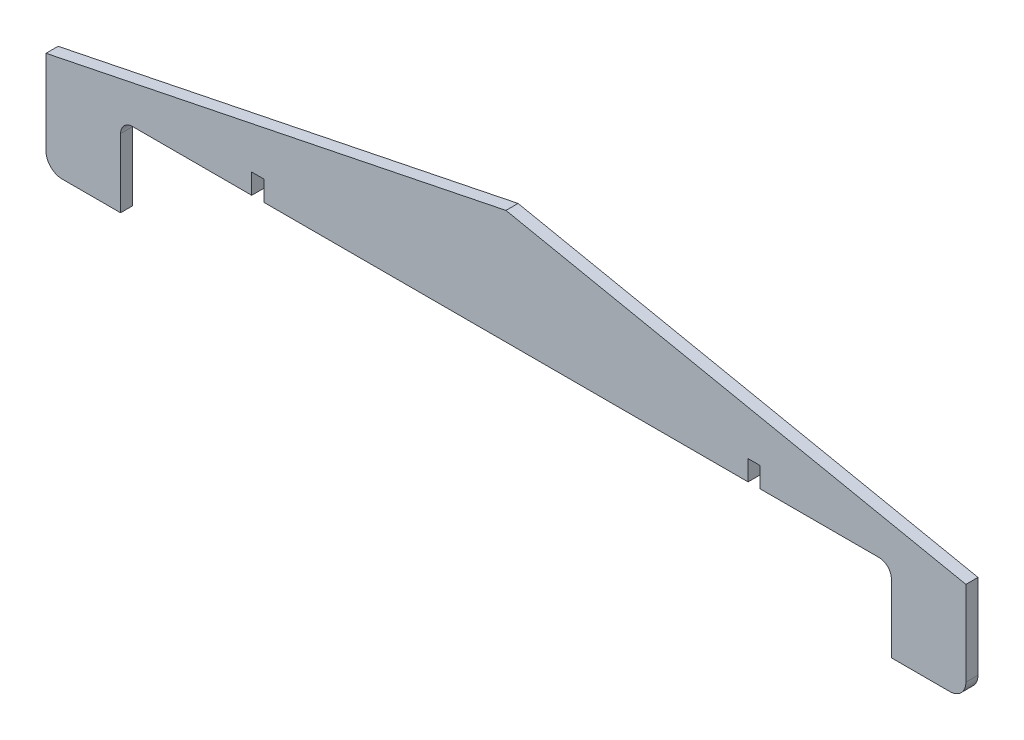
SolidWorks part; units mm, degrees
ref_plane "Front Plane" through (0, 0, 0) normal (0, 0, 1) x (1, 0, 0)
ref_plane "Top Plane" through (0, 0, 0) normal (0, 1, 0) x (1, 0, 0)
ref_plane "Right Plane" through (0, 0, 0) normal (1, 0, 0) x (0, 0, -1)
sketch "Sketch1" plane through (0, 0, 0) normal (0, 0, 1) x (1, 0, 0)
  line L0 (0, 0) -> (0, 19.9998) construction
  line L1 (-16, 19.9998) -> (16, 19.9998)
  line L2 (-113.9796, 0) -> (-113.9796, -25)
  line L4 (113.9796, 0) -> (113.9796, -25)
  line L6 (-113.9796, -7.3549) -> (0, 0) construction
  line L7 (0, 19.9998) -> (0, -25) construction
  line L8 (0, -25) -> (0, 0) construction
  line L9 (0, 0) -> (-113.9796, 0) construction
  line L10 (-113.9796, 0) -> (113.9796, 0) construction
  line L11 (-113.9796, 0) -> (-16, 19.9998)
  line L12 (16, 19.9998) -> (113.9796, 0)
  line L13 (-113.9796, -25) -> (113.9796, -25)
  point P0 (0, 0)
  dimension "D1" = 16
  dimension "D2" = 227.9593
  dimension "D3" = 100
  dimension "D4" = 25
extrude "Boss-Extrude1" add sketch "Sketch1" along normal blind 3
sketch "Sketch2" plane through (0, 0, 3) normal (0, 0, 1) x (1, 0, 0)
  line L0 (0, 0) -> (0, -25) construction
  line L1 (-113.9796, -25) -> (113.9796, -25) construction
  line L2 (0, -25) -> (0, -35.2092) construction
  line L4 (-95.5, -5) -> (95.5, -5)
  line L5 (-95.5, -5) -> (-95.5, -45)
  line L6 (-95.5, -45) -> (95.5, -45)
  line L7 (95.5, -5) -> (95.5, -45)
  line L8 (-95.5, -5) -> (95.5, -45) construction
  line L9 (-95.5, -45) -> (95.5, -5) construction
  dimension "D1" = 191
  dimension "D2" = 20
extrude "Cut-Extrude1" cut sketch "Sketch2" against normal through all
fillet "Fillet1" radius 3 2 edges at (95.5, -5, 1.5) (-95.5, -5, 1.5)
sketch "Sketch3" plane through (0, 0, 3) normal (0, 0, 1) x (1, 0, 0)
  line L0 (0, -5) -> (0, 19.9998) construction
  line L2 (92.5, -5) -> (-92.5, -5) construction
  line L3 (-60, -10) -> (-63, -10)
  line L4 (-60, -10) -> (-60, 0)
  line L5 (-60, 0) -> (-63, 0)
  line L6 (-63, -10) -> (-63, 0)
  line L7 (-60, -10) -> (-63, 0) construction
  line L8 (-60, 0) -> (-63, -10) construction
  line L9 (16, 19.9998) -> (-16, 19.9998) construction
  line L10 (60, -10) -> (63, -10)
  line L11 (60, -10) -> (60, 0)
  line L12 (60, 0) -> (63, 0)
  line L13 (63, -10) -> (63, 0)
  line L14 (60, -10) -> (63, 0) construction
  line L15 (60, 0) -> (63, -10) construction
  point P0 (-61.5, -5)
  point P3 (0, -5)
  point P11 (61.5, -5)
  dimension "D1" = 3
  dimension "D2" = 3
  dimension "D3" = 10
  dimension "D4" = 10
  dimension "D5" = 60
  dimension "D6" = 60
extrude "Cut-Extrude2" cut sketch "Sketch3" against normal through all
fillet "Fillet2" radius 4 2 edges at (113.9796, -25, 1.5) (-113.9796, -25, 1.5)
sketch "Sketch4" plane through (0, 0, 3) normal (0, 0, 1) x (1, 0, 0)
  line L0 (-26.2944, 17.8985) -> (0, 23.2658)
  line L2 (26.8113, 17.793) -> (0, 23.2658)
  line L4 (-26.2944, 17.8985) -> (26.8113, 17.793)
extrude "Boss-Extrude2" add sketch "Sketch4" against normal up to surface (3 mm away) up to face at (0, -6.7461, 0)
